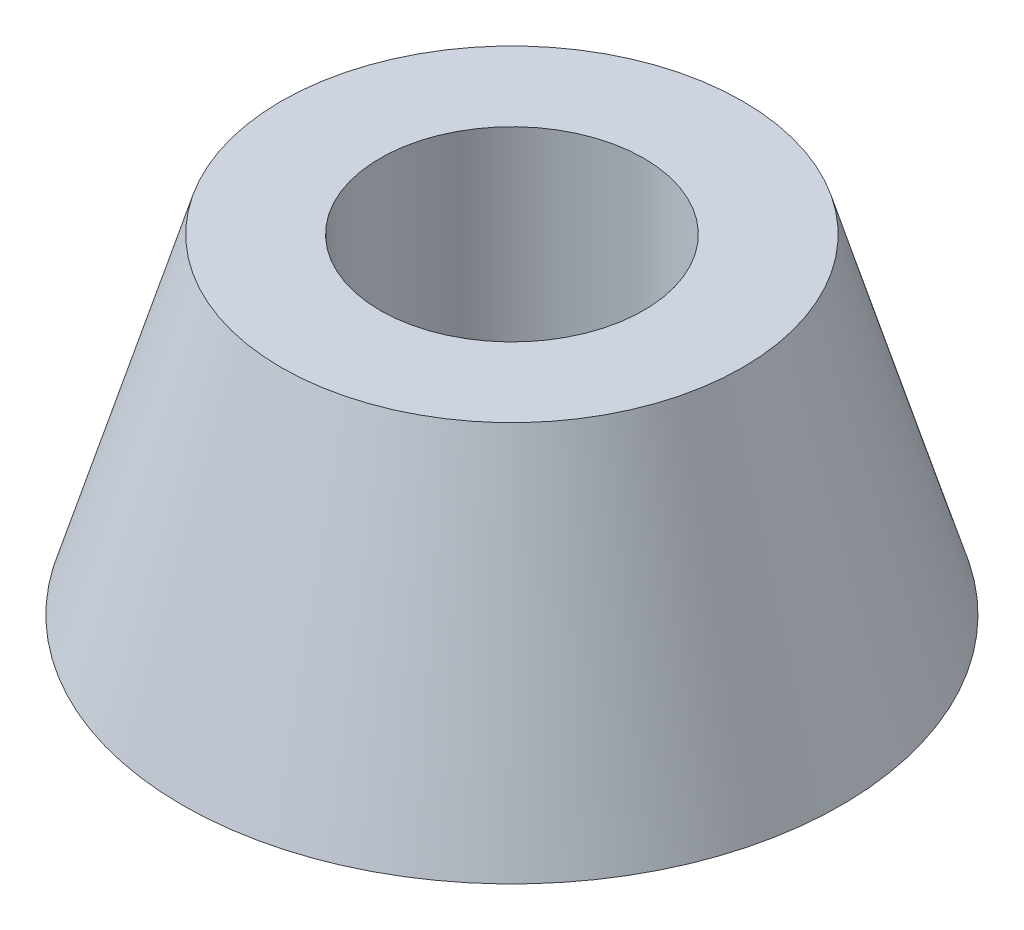
SolidWorks part; units mm, degrees
ref_plane "Front Plane" through (0, 0, 0) normal (0, 0, 1) x (1, 0, 0)
ref_plane "Top Plane" through (0, 0, 0) normal (0, 1, 0) x (1, 0, 0)
ref_plane "Right Plane" through (0, 0, 0) normal (1, 0, 0) x (0, 0, -1)
sketch "Sketch1" plane through (0, 0, 0) normal (0, 1, 0) x (1, 0, 0)
  circle A0 centre (0, 0) radius 10
  dimension "D1" = 20
extrude "Boss-Extrude1" add sketch "Sketch1" along normal blind 10 draft 16.699
sketch "Sketch2" plane through (0, 10, 0) normal (0, 1, 0) x (1, 0, 0)
  circle A0 centre (0, 0) radius 4
  dimension "D1" = 8
extrude "Cut-Extrude1" cut sketch "Sketch2" against normal blind 7
sketch "Sketch3" plane through (0, 3, 0) normal (0, 1, 0) x (1, 0, 0)
  circle A0 centre (0, 0) radius 2.5
  dimension "D1" = 5
extrude "Cut-Extrude2" cut sketch "Sketch3" against normal through all
